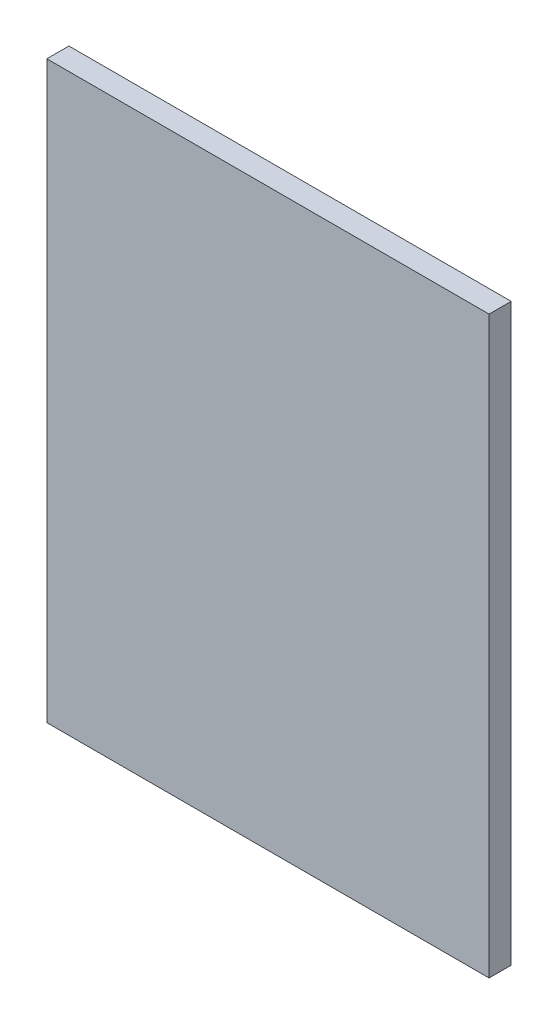
SolidWorks part; units mm, degrees
ref_plane "Front Plane" through (0, 0, 0) normal (0, 0, 1) x (1, 0, 0)
ref_plane "Top Plane" through (0, 0, 0) normal (0, 1, 0) x (1, 0, 0)
ref_plane "Right Plane" through (0, 0, 0) normal (1, 0, 0) x (0, 0, -1)
sketch "Sketch1" plane through (0, 0, 0) normal (0, 0, 1) x (1, 0, 0)
  line L1 (50, -65) -> (-50, -65)
  line L2 (50, -65) -> (50, 65)
  line L3 (50, 65) -> (-50, 65)
  line L4 (-50, -65) -> (-50, 65)
  line L5 (50, -65) -> (-50, 65) construction
  line L6 (50, 65) -> (-50, -65) construction
  point P0 (0, 0)
  dimension "D1" = 100
  dimension "D2" = 130
extrude "Boss-Extrude1" add sketch "Sketch1" along normal blind 5
